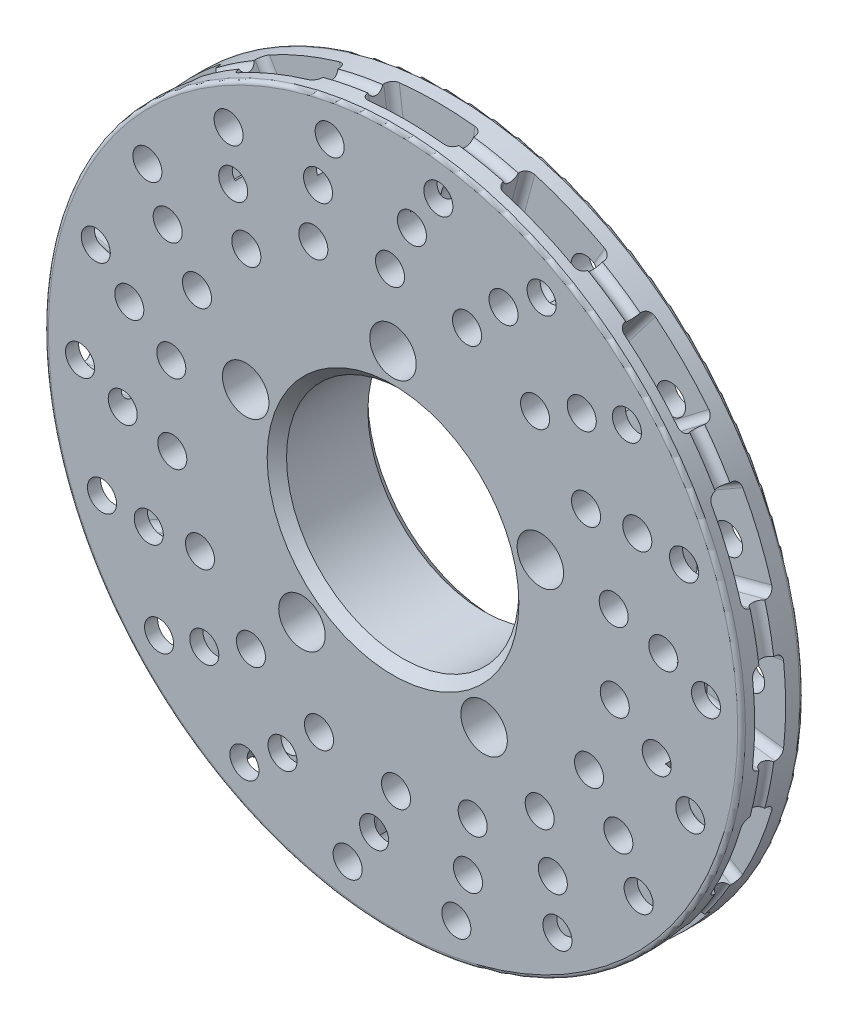
SolidWorks part; units mm, degrees
ref_plane "Front Plane" through (0, 0, 0) normal (0, 0, 1) x (1, 0, 0)
ref_plane "Top Plane" through (0, 0, 0) normal (0, 1, 0) x (1, 0, 0)
ref_plane "Right Plane" through (0, 0, 0) normal (1, 0, 0) x (0, 0, -1)
sketch "Sketch1" plane through (0, 0, 0) normal (0, 0, 1) x (1, 0, 0)
  circle A1 centre (0, 0) radius 90
  circle A2 centre (0, 0) radius 30
  dimension "D1" = 180
  dimension "D2" = 60
extrude "Boss-Extrude1" add sketch "Sketch1" along normal mid plane 16
sketch "Sketch2" plane through (0, 0, -8) normal (0, 0, -1) x (-1, 0, 0)
  circle A0 centre (0, 0) radius 50
  circle A1 centre (0, 0) radius 30 construction
  circle A2 centre (0, 0) radius 30
  dimension "D1" = 100
extrude "Boss-Extrude2" add sketch "Sketch2" along normal blind 10
sketch "Sketch3" plane through (0, 0, -18) normal (0, 0, -1) x (-1, 0, 0)
  circle A0 centre (0, 0) radius 40
  point P3 (0, 40)
  point P4 (38.0423, 12.3607)
  point P5 (0, 0)
  point P7 (23.5114, -32.3607)
  point P8 (-23.5114, -32.3607)
  point P9 (-38.0423, 12.3607)
  point P10 (0, 0)
  dimension "D1" = 80
  dimension "D2" = 5
hole_wizard "Ø12.0 (12) Diameter Hole1" positions "3DSketch1" profile "Sketch4" hole size "Ø12.0" standard "ISO" end condition through all
sketch3d "3DSketch1"
  point P0 (0, 40, -18)
  point P3 (-38.0423, 12.3607, -18)
  point P6 (-23.5114, -32.3607, -18)
  point P9 (23.5114, -32.3607, -18)
  point P12 (38.0423, 12.3607, -18)
sketch "Sketch4" plane through (0, 40, -18) normal (1, 0, 0) x (0, 1, 0)
  line L0 (0, 0) -> (0, 26)
  line L1 (0, 26) -> (6, 26)
  line L2 (6, 26) -> (6, 0.025)
  line L3 (6, 0.025) -> (6.025, 0)
  line L5 (6.025, 0) -> (0, 0)
  line L6 (-6, 0.025) -> (-6.025, 0) construction
  line L11 (0, -6.35) -> (0, 107.95) construction
  dimension "Thru Hole Dia." = 12
  dimension "Thru Hole Depth" = 26
  dimension "Near C'Sink Dia." = 12.05
  dimension "Near C'Sink Angle" = 90
sketch "Sketch5" plane through (0, 0, 0) normal (1, 0, 0) x (0, 0, -1)
  line L0 (8, 90) -> (-8, 90) construction
  line L1 (-4.6218, 90) -> (3.3782, 90)
  line L2 (-4.6218, 90) -> (-4.6218, 70)
  line L3 (-4.6218, 70) -> (3.3782, 70)
  line L4 (3.3782, 90) -> (3.3782, 70)
  line L5 (0, 0) -> (-8, 0) construction
  line L6 (-8, 90) -> (-8, -90) construction
  dimension "D1" = 20
  dimension "D2" = 8
revolve "Cut-Revolve1" cut sketch "Sketch5" angle 15 mid plane about L5
fillet "Fillet1" radius 2 4 edges at (-10.4421, 79.3156, 4.6218) (10.4421, 79.3156, 4.6218) (-10.4421, 79.3156, -3.3782) (10.4421, 79.3156, -3.3782)
pattern_circular "CirPattern1" count 16 over 360 about axis through (0, 0, 0) along (0, 0, 1) of "Fillet1", "Cut-Revolve1"
sketch "Sketch6" plane through (0, 0, -8) normal (0, 0, -1) x (-1, 0, 0)
  arc A0 (0, 0) -> (-19.0262, 87.9659) centre (-74.162, 30) ccw construction
  circle A1 centre (0, 0) radius 90 construction
  point P3 (0.778, 58)
  point P7 (-4.88, 70)
  point P8 (-11.712, 80)
  dimension "D2" = 80
  dimension "D1" = 30
  dimension "D3" = 80
  dimension "D4" = 10
  dimension "D5" = 12
hole_wizard "Ø7.5 (7.5) Diameter Hole1" positions "3DSketch3" profile "Sketch8" hole size "Ø7.5" standard "ISO" end condition through all
sketch3d "3DSketch3"
  point P0 (11.712, 80, -8)
  point P3 (4.88, 70, -8)
  point P6 (-0.778, 58, -8)
sketch "Sketch8" plane through (11.712, 80, -8) normal (1, 0, 0) x (0, 1, 0)
  line L0 (0, 0) -> (0, 16)
  line L1 (0, 16) -> (3.75, 16)
  line L2 (3.75, 16) -> (3.75, 0.025)
  line L3 (3.75, 0.025) -> (3.775, 0)
  line L5 (3.775, 0) -> (0, 0)
  line L6 (-3.75, 0.025) -> (-3.775, 0) construction
  line L11 (0, -6.35) -> (0, 107.95) construction
  dimension "Thru Hole Dia." = 7.5
  dimension "Thru Hole Depth" = 16
  dimension "Near C'Sink Dia." = 7.55
  dimension "Near C'Sink Angle" = 90
pattern_circular "CirPattern2" count 18 over 360 about axis through (0, 0, 0) along (0, 0, 1) of "Ø7.5 (7.5) Diameter Hole1"
sketch "Sketch9" plane through (0, 0, 0) normal (1, 0, 0) x (0, 0, -1)
  line L1 (0, 0) -> (8, 0) construction
  line L3 (8, -90) -> (8, 90) construction
  circle A0 centre (-0.846, 90.5952) radius 2
  point P10 (8, 90)
  dimension "D1" = 4
revolve "Cut-Revolve2" cut sketch "Sketch9" angle 360 about L1
fillet "Fillet2" radius 1 4 edges at (90, 0, 8) (90, 0, -8) (-50, 0, -18) (50, 0, -8)
chamfer "Chamfer1" distance 2.5 angle 45 2 edges at (-30, 0, -18) (30, 0, 8)
